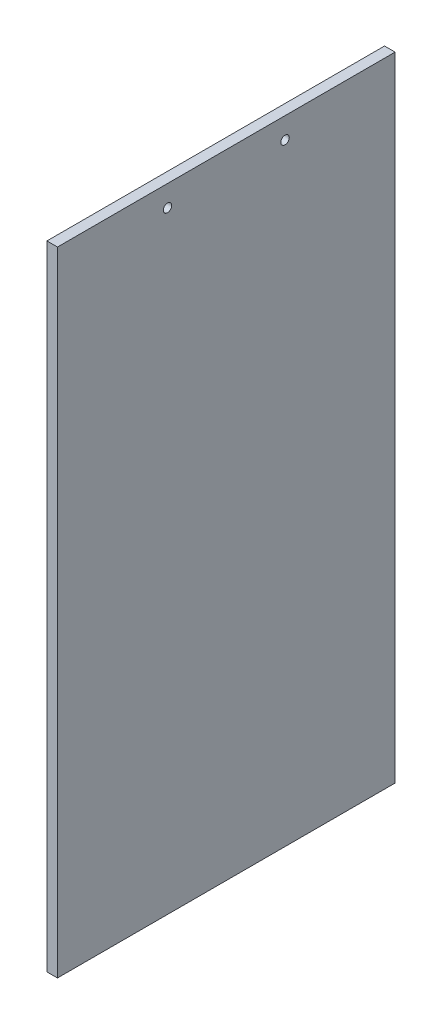
SolidWorks part; units mm, degrees
ref_plane "Front" through (0, 0, 0) normal (0, 0, 1) x (1, 0, 0)
ref_plane "Top" through (0, 0, 0) normal (0, 1, 0) x (1, 0, 0)
ref_plane "Right" through (0, 0, 0) normal (1, 0, 0) x (0, 0, -1)
sketch "草图1" plane through (0, 0, 0) normal (1, 0, 0) x (0, 0, -1)
  line L1 (0, 0) -> (180, 0)
  line L2 (0, 0) -> (0, -300)
  line L3 (0, -300) -> (180, -300)
  line L4 (180, 0) -> (180, -300)
  dimension "D1" = 180
  dimension "D2" = 300
extrude "凸台-拉伸1" add sketch "草图1" along normal blind 5
sketch "草图2" plane through (5, 0, 0) normal (1, 0, 0) x (0, 0, -1)
  line L0 (90, 0) -> (90, -300) construction
  line L1 (180, 0) -> (0, 0) construction
  line L2 (0, -300) -> (180, -300) construction
  circle A0 centre (62.15, -10) radius 2
  circle A1 centre (117.85, -10) radius 2
  dimension "D1" = 4
  dimension "D2" = 4
  dimension "D3" = 55.7
  dimension "D4" = 10
extrude "切除-拉伸1" cut sketch "草图2" against normal up to next
sketch "草图3" plane through (5, 0, 0) normal (1, 0, 0) x (0, 0, -1)
  line L0 (90, 0) -> (90, -300) construction
  line L1 (180, 0) -> (0, 0) construction
  line L2 (0, -300) -> (180, -300) construction
  line L3 (0, 0) -> (0, -300) construction
  line L4 (20, -50) -> (35, -50)
  line L5 (20, -50) -> (20, -250)
  line L6 (20, -250) -> (35, -250)
  line L7 (35, -50) -> (35, -250)
  line L8 (60, -50) -> (75, -50)
  line L9 (60, -50) -> (60, -250)
  line L10 (75, -50) -> (75, -250)
  line L11 (60, -250) -> (75, -250)
  line L12 (120, -250) -> (105, -250)
  line L13 (105, -50) -> (105, -250)
  line L14 (120, -50) -> (120, -250)
  line L15 (120, -50) -> (105, -50)
  line L16 (145, -50) -> (145, -250)
  line L17 (160, -250) -> (145, -250)
  line L18 (160, -50) -> (160, -250)
  line L19 (160, -50) -> (145, -50)
  dimension "D1" = 15
  dimension "D2" = 200
  dimension "D3" = 50
  dimension "D4" = 20
  dimension "D6" = 25
  dimension "D5" = 2
extrude "切除-拉伸2" [suppressed] cut sketch "草图3" against normal up to next
sketch "草图4" plane through (5, 0, 0) normal (1, 0, 0) x (0, 0, -1)
  line L0 (0, -300) -> (180, -300) construction
  line L1 (0, 0) -> (10, 0)
  line L2 (0, 0) -> (0, -300)
  line L3 (0, -300) -> (10, -300)
  line L4 (10, 0) -> (10, -300)
  line L6 (180, 0) -> (170, 0)
  line L7 (180, 0) -> (180, -300)
  line L8 (180, -300) -> (170, -300)
  line L9 (170, 0) -> (170, -300)
  dimension "D1" = 10
  dimension "D2" = 10
extrude "切除-拉伸3" cut sketch "草图4" against normal blind 10
sketch "草图5" plane through (5, 0, 0) normal (1, 0, 0) x (0, 0, -1)
  line L0 (170, 0) -> (170, -300) construction
  line L1 (10, -300) -> (170, -300)
  line L2 (10, -300) -> (10, -270)
  line L3 (10, -270) -> (170, -270)
  line L4 (170, -300) -> (170, -270)
  dimension "D1" = 30
extrude "切除-拉伸5" [suppressed] cut sketch "草图5" against normal blind 10
